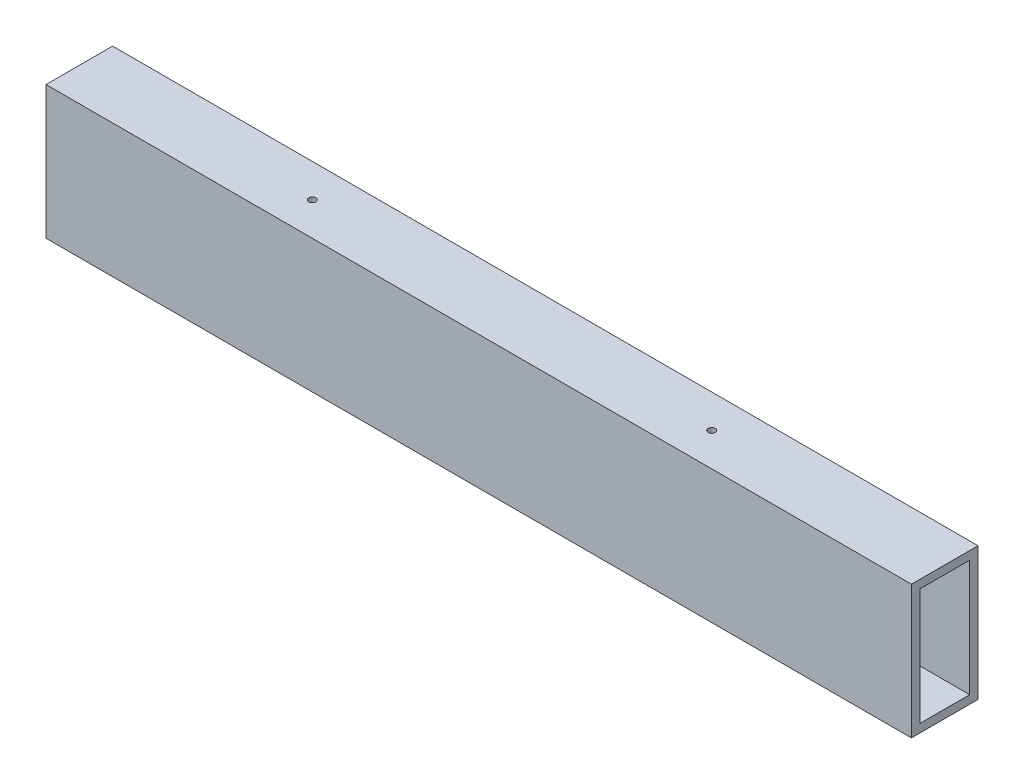
SolidWorks part; units mm, degrees
material "6061 Alloy"
ref_plane "Front Plane" through (0, 0, 0) normal (0, 0, 1) x (1, 0, 0)
ref_plane "Top Plane" through (0, 0, 0) normal (0, 1, 0) x (1, 0, 0)
ref_plane "Right Plane" through (0, 0, 0) normal (1, 0, 0) x (0, 0, -1)
sketch "Sketch1" plane through (0, 0, 0) normal (1, 0, 0) x (0, 0, -1)
  line L0 (-9.525, 22.225) -> (9.525, 22.225)
  line L1 (-12.7, -25.4) -> (12.7, -25.4)
  line L2 (-12.7, -25.4) -> (-12.7, 25.4)
  line L3 (-12.7, 25.4) -> (12.7, 25.4)
  line L4 (12.7, -25.4) -> (12.7, 25.4)
  line L5 (-12.7, -25.4) -> (12.7, 25.4) construction
  line L6 (-12.7, 25.4) -> (12.7, -25.4) construction
  line L7 (9.525, -22.225) -> (9.525, 22.225)
  line L8 (-9.525, -22.225) -> (9.525, -22.225)
  line L9 (-9.525, -22.225) -> (-9.525, 22.225)
  point P0 (0, 0)
  dimension "D1" = 25.4
  dimension "D2" = 50.8
  dimension "D3" = 3.175
extrude "Boss-Extrude1" add sketch "Sketch1" along normal blind 330.2
sketch "Sketch4" [suppressed] plane through (0, 0, 12.7) normal (0, 0, 1) x (1, 0, 0)
  line L0 (0, 0) -> (304.8, 0) construction
  line L1 (304.8, 25.4) -> (304.8, -25.4) construction
  line L2 (0, 25.4) -> (0, -25.4) construction
  circle A0 centre (63.5, 0) radius 6.35
  circle A1 centre (224.0534, 0) radius 6.35
  dimension "D1" = 12.7
  dimension "D3" = 160.5534
  dimension "D2" = 63.5
extrude "Cut-Extrude1" [suppressed] cut sketch "Sketch4" against normal up to next
sketch "Sketch5" [suppressed] plane through (0, 0, -12.7) normal (0, 0, -1) x (-1, 0, 0)
  line L0 (-224.0534, 0) -> (-63.5, 0) construction
  line L4 (0, -25.4) -> (0, 25.4)
  line L5 (0, 25.4) -> (-304.8, 25.4)
  line L6 (-304.8, 25.4) -> (-304.8, -25.4)
  line L7 (-304.8, -25.4) -> (0, -25.4)
  line L8 (0, -25.4) -> (0, 25.4)
  line L9 (0, 25.4) -> (-304.8, 25.4)
  line L10 (-304.8, 25.4) -> (-304.8, -25.4)
  line L11 (-304.8, -25.4) -> (0, -25.4)
  circle A1 centre (-63.5, 0) radius 6.35 construction
  circle A2 centre (-224.0534, 0) radius 6.35 construction
  circle A3 centre (-224.0534, 0) radius 6.35 construction
  circle A4 centre (-224.0534, 0) radius 6.35
  circle A5 centre (-63.5, 0) radius 6.35
  point P20 (-41.275, -15.875)
  point P21 (-104.775, 15.875)
  point P22 (-41.275, 15.875)
  point P24 (-104.775, -15.875)
  dimension "D2" = 12.7
  dimension "D3" = 63.5
  dimension "D4" = 31.75
  dimension "D5" = 63.5
  dimension "D6" = 25.4
  dimension "D7" = 22.225
  dimension "D1" = 0
extrude "Cut-Extrude2" [suppressed] cut sketch "Sketch5" against normal up to next
sketch "Sketch6" [suppressed] plane through (0, 25.4, 0) normal (0, 1, 0) x (1, 0, 0)
  line L0 (63.5, 12.7) -> (63.5, -12.7) construction
  line L1 (304.8, 12.7) -> (0, 12.7) construction
  line L2 (304.8, -12.7) -> (0, -12.7) construction
  line L3 (57.15, -12.7) -> (69.85, -12.7) construction
  line L4 (224.0534, 12.7) -> (224.0534, -12.7) construction
  line L5 (217.7034, -12.7) -> (230.4034, -12.7) construction
  line L6 (304.8, 9.525) -> (0, 9.525) construction
  line L7 (233.5784, 9.525) -> (53.975, 9.525)
  line L8 (304.8, -9.525) -> (0, -9.525) construction
  line L9 (233.5784, -9.525) -> (53.975, -9.525)
  line L10 (50.8, 6.35) -> (50.8, -6.35)
  line L11 (236.7534, 6.35) -> (236.7534, -6.35)
  arc A0 (233.5784, -9.525) -> (236.7534, -6.35) centre (233.5784, -6.35) ccw
  arc A1 (236.7534, 6.35) -> (233.5784, 9.525) centre (233.5784, 6.35) ccw
  arc A2 (53.975, -9.525) -> (50.8, -6.35) centre (53.975, -6.35) cw
  arc A3 (50.8, 6.35) -> (53.975, 9.525) centre (53.975, 6.35) cw
  dimension "D3" = 3.175
  dimension "D1" = 12.7
  dimension "D2" = 12.7
extrude "Cut-Extrude3" [suppressed] cut sketch "Sketch6" against normal up to next
sketch "Sketch7" [suppressed] plane through (0, 0, -12.7) normal (0, 0, -1) x (-1, 0, 0)
  line L0 (-304.8, 0) -> (0, 0) construction
  line L1 (-304.8, -25.4) -> (-304.8, 25.4) construction
  line L2 (-285.75, 25.4) -> (-285.75, -25.4) construction
  line L3 (-304.8, 25.4) -> (0, 25.4) construction
  line L4 (-304.8, -25.4) -> (0, -25.4) construction
  line L5 (-276.5576, 9.1924) -> (-294.9424, -9.1924) construction
  line L6 (-294.9424, 9.1924) -> (-276.5576, -9.1924) construction
  circle A0 centre (-285.75, 0) radius 3.5
  point P18 (-294.9424, 9.1924)
  point P19 (-276.5576, 9.1924)
  point P20 (-276.5576, -9.1924)
  point P21 (-294.9424, -9.1924)
  dimension "D1" = 7
  dimension "D2" = 45
  dimension "D3" = 45
  dimension "D4" = 26
  dimension "D5" = 26
  dimension "D6" = 19.05
extrude "Cut-Extrude4" [suppressed] cut sketch "Sketch7" against normal up to next
hole_wizard "#6-32 Tapped Hole3" [suppressed] positions "3DSketch1" profile "Sketch8" tap size "#6-32" standard "ANSI Inch"
sketch3d "3DSketch1"
  point P0 (129.8424, 9.1924, -12.7)
  point P3 (111.4576, 9.1924, -12.7)
  point P6 (111.4576, -9.1924, -12.7)
  point P9 (129.8424, -9.1924, -12.7)
sketch "Sketch8" plane through (0, 0, 0) normal (0, 0, 1) x (1, 0, 0)
  line L0 (0, 0) -> (0, 3.175)
  line L1 (0, 3.175) -> (1.3525, 3.175)
  line L2 (1.3525, 3.175) -> (1.3525, 0)
  line L5 (1.3525, 0) -> (0, 0)
  line L11 (0, -6.35) -> (0, 107.95) construction
  dimension "Thread Major Dia." = 2.7051
  dimension "Thru Tap Drill Depth" = 3.175
sketch "Sketch9" [suppressed] plane through (0, 0, 12.7) normal (0, 0, 1) x (1, 0, 0)
  line L0 (129.8424, 9.1924) -> (111.4576, -9.1924) construction
  line L1 (34.5924, 12.3674) -> (34.5924, -12.3674)
  line L2 (37.7674, -15.5424) -> (133.0174, -15.5424)
  line L4 (37.7674, 15.5424) -> (133.0174, 15.5424)
  line L5 (136.1924, -12.3674) -> (136.1924, 12.3674)
  line L6 (105.1076, -15.5424) -> (136.1924, 15.5424) construction
  line L7 (105.1076, 15.5424) -> (136.1924, -15.5424) construction
  circle A0 centre (111.4576, -9.1924) radius 1.7 construction
  circle A1 centre (129.8424, -9.1924) radius 1.7 construction
  circle A2 centre (129.8424, 9.1924) radius 1.7 construction
  circle A3 centre (111.4576, 9.1924) radius 1.7 construction
  circle A4 centre (111.4576, -9.1924) radius 1.7 construction
  circle A5 centre (129.8424, -9.1924) radius 1.7 construction
  circle A6 centre (129.8424, 9.1924) radius 1.7 construction
  circle A7 centre (111.4576, 9.1924) radius 1.7 construction
  arc A8 (133.0174, 15.5424) -> (136.1924, 12.3674) centre (133.0174, 12.3674) cw
  arc A9 (136.1924, -12.3674) -> (133.0174, -15.5424) centre (133.0174, -12.3674) cw
  arc A12 (37.7674, -15.5424) -> (34.5924, -12.3674) centre (37.7674, -12.3674) cw
  arc A13 (34.5924, 12.3674) -> (37.7674, 15.5424) centre (37.7674, 12.3674) cw
  point P12 (120.65, 0)
  dimension "D3" = 3.175
  dimension "D4" = 3.175
  dimension "D1" = 6.35
  dimension "D2" = 101.6
extrude "Cut-Extrude5" [suppressed] cut sketch "Sketch9" against normal up to next
hole_wizard "#6-32 Tapped Hole1" [suppressed] positions "3DSketch2" profile "Sketch10" tap size "#6-32" standard "ANSI Inch"
sketch3d "3DSketch2"
  point P0 (104.775, 15.875, -12.7)
  point P3 (41.275, 15.875, -12.7)
  point P6 (41.275, -15.875, -12.7)
  point P9 (104.775, -15.875, -12.7)
sketch "Sketch10" plane through (104.775, 15.875, -12.7) normal (1, 0, 0) x (0, 1, 0)
  line L0 (0, 0) -> (0, 3.175)
  line L1 (0, 3.175) -> (1.3525, 3.175)
  line L2 (1.3525, 3.175) -> (1.3525, 0)
  line L5 (1.3525, 0) -> (0, 0)
  line L11 (0, -6.35) -> (0, 107.95) construction
  dimension "Thread Major Dia." = 2.7051
  dimension "Thru Tap Drill Depth" = 3.175
sketch "Sketch11" [suppressed] plane through (0, 0, -12.7) normal (0, 0, -1) x (-1, 0, 0)
  line L0 (-95.25, 0) -> (0, 0) construction
  line L1 (-95.25, -25.4) -> (-95.25, 25.4) construction
  line L2 (0, -25.4) -> (0, 25.4) construction
  line L3 (-15.24, 12.7) -> (-12.7, 12.7)
  line L4 (-15.24, -12.7) -> (-12.7, -12.7)
  line L5 (0, -12.7) -> (0, 12.7)
  line L6 (0, 12.7) -> (0, 22.225)
  line L7 (0, 22.225) -> (-12.7, 22.225)
  line L8 (-12.7, 22.225) -> (-12.7, 12.7)
  line L9 (-12.7, -12.7) -> (-12.7, -22.225)
  line L10 (-12.7, -22.225) -> (0, -22.225)
  line L11 (0, -22.225) -> (0, -12.7)
  arc A0 (-15.24, 12.7) -> (-15.24, -12.7) centre (-15.24, 0) ccw
  dimension "D1" = 25.4
  dimension "D2" = 15.24
  dimension "D3" = 12.7
  dimension "D4" = 44.45
extrude "Cut-Extrude6" [suppressed] cut sketch "Sketch11" against normal up to next
sketch "Sketch12" [suppressed] plane through (0, -25.4, 0) normal (0, -1, 0) x (1, 0, 0)
  line L0 (0, 0) -> (304.8, 0) construction
  line L1 (304.8, 12.7) -> (304.8, -12.7) construction
  line L2 (152.4, 0) -> (152.4, 12.7) construction
  line L3 (304.8, 12.7) -> (0, 12.7) construction
  line L4 (0, 12.7) -> (0, -12.7) construction
  point P5 (12.7, 0)
  point P6 (292.1, 0)
  point P7 (209.55, 0)
  point P8 (95.25, 0)
  dimension "D1" = 114.3
  dimension "D2" = 12.7
hole_wizard "#6-32 Tapped Hole2" [suppressed] positions "3DSketch3" profile "Sketch13" tap size "#6-32" standard "ANSI Inch"
sketch3d "3DSketch3"
  point P1 (12.7, -25.4, 0)
  point P4 (95.25, -25.4, 0)
  point P7 (209.55, -25.4, 0)
  point P10 (292.1, -25.4, 0)
sketch "Sketch13" plane through (12.7, -25.4, 0) normal (1, 0, 0) x (0, 0, -1)
  line L0 (0, 0) -> (0, 50.8)
  line L1 (0, 50.8) -> (1.3525, 50.8)
  line L2 (1.3525, 50.8) -> (1.3525, 0)
  line L5 (1.3525, 0) -> (0, 0)
  line L11 (0, -6.35) -> (0, 107.95) construction
  dimension "Thread Major Dia." = 2.7051
  dimension "Thru Tap Drill Depth" = 50.8
sketch "Sketch14" [suppressed] plane through (0, -25.4, 0) normal (0, -1, 0) x (1, 0, 0)
  line L0 (0, 0) -> (177.8, 0) construction
  line L1 (177.8, 12.7) -> (177.8, -12.7) construction
  point P5 (88.9, 0)
hole_wizard "#6-32 Tapped Hole4" [suppressed] positions "3DSketch4" profile "Sketch15" tap size "#6-32" standard "ANSI Inch"
sketch3d "3DSketch4"
  point P0 (88.9, -25.4, 0)
sketch "Sketch15" plane through (88.9, -25.4, 0) normal (1, 0, 0) x (0, 0, -1)
  line L0 (0, 0) -> (0, 50.8)
  line L1 (0, 50.8) -> (1.3525, 50.8)
  line L2 (1.3525, 50.8) -> (1.3525, 0)
  line L5 (1.3525, 0) -> (0, 0)
  line L11 (0, -6.35) -> (0, 107.95) construction
  dimension "Thread Major Dia." = 2.7051
  dimension "Thru Tap Drill Depth" = 50.8
sketch "Sketch16" [suppressed] plane through (0, -25.4, 0) normal (0, -1, 0) x (1, 0, 0)
  line L0 (0, -7.9248) -> (139.7, -7.9248) construction
  line L2 (0, 12.7) -> (0, -12.7) construction
  line L4 (95.25, -12.7) -> (0, -12.7) construction
  point P5 (4.7752, -7.9248)
  dimension "D1" = 4.7752
  dimension "D2" = 4.7752
hole_wizard "#6-32 Tapped Hole5" [suppressed] positions "3DSketch5" profile "Sketch17" tap size "#6-32" standard "ANSI Inch"
sketch3d "3DSketch5"
  point P0 (4.7752, -25.4, -7.9248)
sketch "Sketch17" plane through (4.7752, -25.4, -7.9248) normal (1, 0, 0) x (0, 0, -1)
  line L0 (0, 0) -> (0, 50.8)
  line L1 (0, 50.8) -> (1.3525, 50.8)
  line L2 (1.3525, 50.8) -> (1.3525, 0)
  line L5 (1.3525, 0) -> (0, 0)
  line L11 (0, -6.35) -> (0, 107.95) construction
  dimension "Thread Major Dia." = 2.7051
  dimension "Thru Tap Drill Depth" = 50.8
sketch "Sketch18" plane through (0, -25.4, 0) normal (0, -1, 0) x (1, 0, 0)
  line L0 (0, 0) -> (330.2, 0) construction
  line L1 (330.2, 12.7) -> (330.2, -12.7) construction
  line L2 (165.1, 0) -> (165.1, 12.7) construction
  line L3 (330.2, 12.7) -> (0, 12.7) construction
  point P5 (88.9, 0)
  point P6 (241.3, 0)
  dimension "D1" = 152.4
hole_wizard "#6-32 Tapped Hole6" positions "3DSketch6" profile "Sketch19" tap size "#6-32" standard "ANSI Inch" end condition through all
sketch3d "3DSketch6"
  point P0 (88.9, -25.4, 0)
  point P3 (241.3, -25.4, 0)
sketch "Sketch19" plane through (88.9, -25.4, 0) normal (1, 0, 0) x (0, 0, -1)
  line L0 (0, 0) -> (0, 50.8)
  line L1 (0, 50.8) -> (1.3525, 50.8)
  line L2 (1.3525, 50.8) -> (1.3525, 0)
  line L5 (1.3525, 0) -> (0, 0)
  line L11 (0, -6.35) -> (0, 107.95) construction
  dimension "Thread Major Dia." = 2.7051
  dimension "Thru Tap Drill Depth" = 50.8
sketch "Sketch20" [suppressed] plane through (0, 0, 12.7) normal (0, 0, 1) x (1, 0, 0)
  line L0 (44.45, 25.4) -> (44.45, -25.4) construction
  line L1 (50.8, 25.4) -> (0, 25.4) construction
  line L2 (50.8, -25.4) -> (0, -25.4) construction
  line L3 (50.8, 25.4) -> (50.8, -25.4) construction
  line L4 (0, 0) -> (44.45, 0) construction
  point P8 (44.45, 12.7)
  point P9 (44.45, -12.7)
  dimension "D1" = 6.35
  dimension "D2" = 25.4
hole_wizard "M3x0.5 Tapped Hole5" [suppressed] positions "3DSketch7" profile "Sketch21" tap size "M3x0.5" standard "ANSI Metric"
sketch3d "3DSketch7"
  point P5 (44.45, 12.7, 12.7)
  point P8 (44.45, -12.7, 12.7)
sketch "Sketch21" plane through (44.45, 12.7, 12.7) normal (1, 0, 0) x (0, -1, 0)
  line L0 (0, 0) -> (0, 3.175)
  line L1 (0, 3.175) -> (1.25, 3.175)
  line L2 (1.25, 3.175) -> (1.25, 0)
  line L5 (1.25, 0) -> (0, 0)
  line L11 (0, -6.35) -> (0, 107.95) construction
  dimension "Thread Major Dia." = 2.5
  dimension "Thru Tap Drill Depth" = 3.175
fillet "Fillet1" [suppressed] radius 3.175
equation "\"D2@Sketch6\"=\"D1@Sketch6\""
equation "\"D5@Sketch7\"=\"D4@Sketch7\""
equation "\"D4@Sketch9\"=\"D3@Sketch9\""
